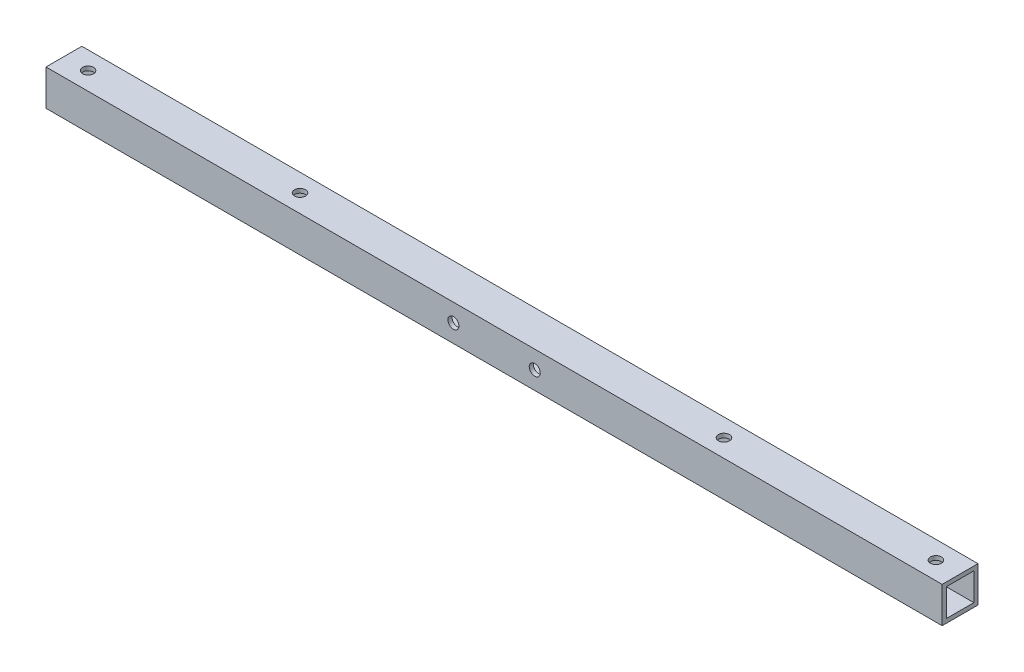
SolidWorks part; units mm, degrees
ref_plane "Front Plane" through (0, 0, 0) normal (0, 0, 1) x (1, 0, 0)
ref_plane "Top Plane" through (0, 0, 0) normal (0, 1, 0) x (1, 0, 0)
ref_plane "Right Plane" through (0, 0, 0) normal (1, 0, 0) x (0, 0, -1)
sketch "Sketch1" plane through (0, 0, 0) normal (0, 1, 0) x (1, 0, 0)
  line L1 (-325, 13) -> (325, 13)
  line L2 (-325, 13) -> (-325, -13)
  line L3 (-325, -13) -> (325, -13)
  line L4 (325, 13) -> (325, -13)
  line L5 (-325, 13) -> (325, -13) construction
  line L6 (-325, -13) -> (325, 13) construction
  point P0 (0, 0)
  dimension "D1" = 26
  dimension "D2" = 650
extrude "Boss-Extrude1" add sketch "Sketch1" along normal blind 26
shell "Shell1" thickness 3
sketch "Sketch2" plane through (0, 26, 0) normal (0, 1, 0) x (1, 0, 0)
  line L0 (325, -13) -> (325, 13) construction
  line L1 (0, -13) -> (0, 13) construction
  line L2 (-325, -13) -> (325, -13) construction
  line L3 (325, 13) -> (-325, 13) construction
  line L4 (307.5, 0) -> (0, 0) construction
  circle A0 centre (307.5, 0) radius 4
  circle A1 centre (-307.5, 0) radius 4
  circle A2 centre (153.75, 0) radius 4
  circle A3 centre (-153.75, 0) radius 4
  dimension "D1" = 8
  dimension "D3" = 8
  dimension "D2" = 17.5
extrude "Cut-Extrude1" cut sketch "Sketch2" against normal blind 26
sketch "Sketch3" plane through (0, 0, 13) normal (0, 0, 1) x (1, 0, 0)
  circle A0 centre (-29.5, 13) radius 4
  circle A1 centre (29.5, 13) radius 4
extrude "Cut-Extrude2" cut sketch "Sketch3" against normal through all
